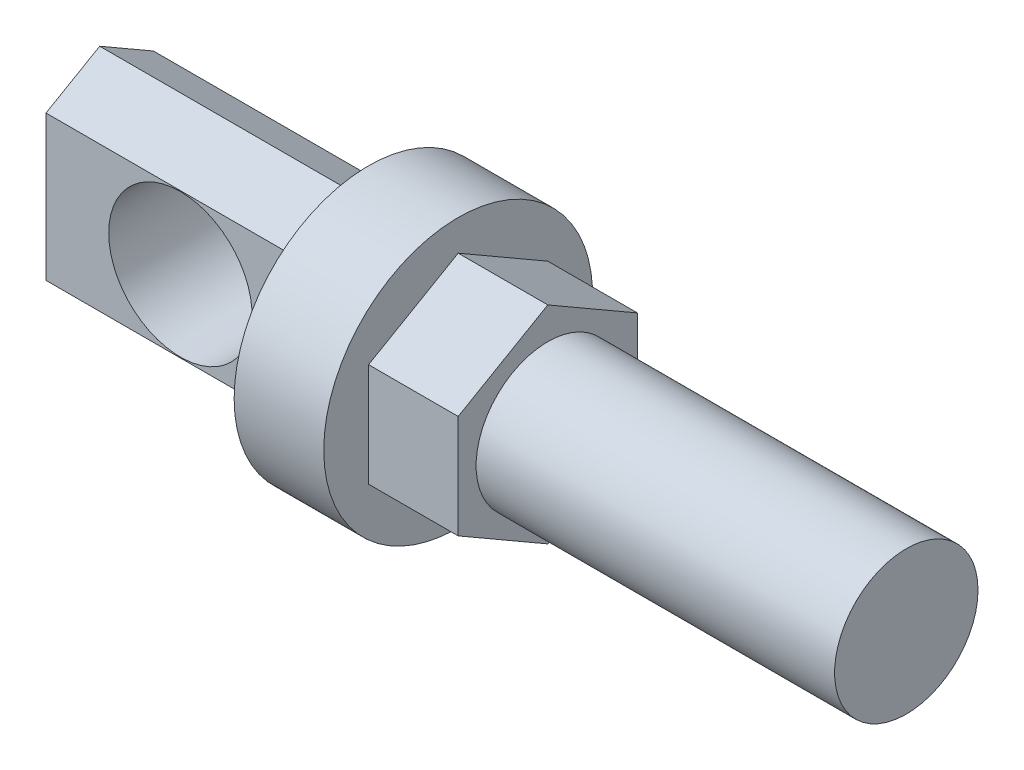
SolidWorks part; units mm, degrees
material "Простая углеродистая сталь"
ref_plane "Спереди" through (0, 0, 0) normal (0, 0, 1) x (1, 0, 0)
ref_plane "Сверху" through (0, 0, 0) normal (0, 1, 0) x (1, 0, 0)
ref_plane "Справа" through (0, 0, 0) normal (1, 0, 0) x (0, 0, -1)
sketch "Эскиз1" plane through (0, 0, 0) normal (1, 0, 0) x (0, 0, -1)
  line L1 (0, 11.547) -> (-10, 5.7735)
  line L2 (-10, 5.7735) -> (-10, -5.7735)
  line L3 (-10, -5.7735) -> (0, -11.547)
  line L4 (0, -11.547) -> (10, -5.7735)
  line L5 (10, -5.7735) -> (10, 5.7735)
  line L6 (10, 5.7735) -> (0, 11.547)
  circle A0 centre (0, 0) radius 10 construction
extrude "Бобышка-Вытянуть1" add sketch "Эскиз1" along normal blind 10
sketch "Эскиз2" plane through (10, 0, 0) normal (1, 0, 0) x (0, 0, -1)
  circle A0 centre (0, 0) radius 8
extrude "Бобышка-Вытянуть2" add sketch "Эскиз2" along normal blind 40
sketch "Эскиз5" plane through (0, 0, 0) normal (-1, 0, 0) x (0, 0, 1)
  circle A0 centre (0, 0) radius 15
extrude "Бобышка-Вытянуть4" add sketch "Эскиз5" along normal blind 10
sketch "Эскиз3" plane through (-10, 0, 0) normal (-1, 0, 0) x (0, 0, 1)
  line L0 (0, 11.547) -> (-6.0017, 8.0819)
  line L2 (-6.0017, 8.0819) -> (-6.0017, -8.0819)
  line L5 (-6.0017, -8.0819) -> (0, -11.547)
  line L6 (0, -11.547) -> (5.9916, -8.0877)
  line L8 (5.9916, -8.0877) -> (5.9916, 8.0877)
  line L10 (5.9916, 8.0877) -> (0, 11.547)
extrude "Бобышка-Вытянуть3" add sketch "Эскиз3" along normal blind 30
sketch "Эскиз4" plane through (0, 0, -6.0017) normal (0, 0, -1) x (-1, 0, 0)
  circle A0 centre (25, 0) radius 8
extrude "Вырез-Вытянуть1" cut sketch "Эскиз4" against normal up to next
